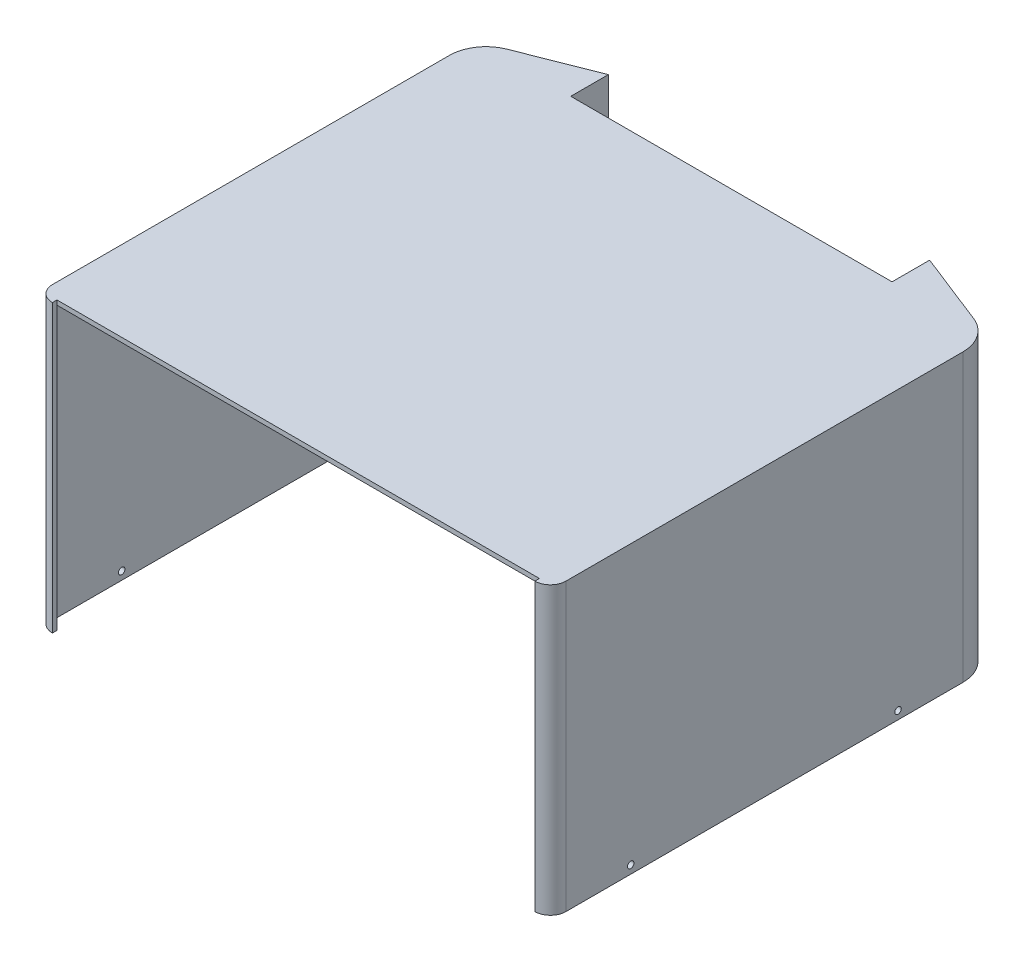
SolidWorks part; units mm, degrees
ref_plane "Front Plane" through (0, 0, 0) normal (0, 0, 1) x (1, 0, 0)
ref_plane "Top Plane" through (0, 0, 0) normal (0, 1, 0) x (1, 0, 0)
ref_plane "Right Plane" through (0, 0, 0) normal (1, 0, 0) x (0, 0, -1)
sketch "Sketch1" plane through (0, 0, 0) normal (0, 1, 0) x (1, 0, 0)
  line L0 (-49.6594, 72.6605) -> (48.7721, 72.6605)
  line L1 (-0.4437, -74.1395) -> (-0.4437, 72.6605)
  line L2 (-49.6594, 59.6605) -> (-50.0594, 59.6605) construction
  line L3 (-50.0594, 59.6605) -> (-49.6594, 59.6605) construction
  line L4 (-72.5188, 63.821) -> (-50.0594, 72.6605)
  line L5 (-79.7437, 53.213) -> (-79.7437, -3.8395)
  line L6 (49.1721, 59.6605) -> (48.7721, 59.6605) construction
  line L7 (48.7721, 59.6605) -> (49.1721, 59.6605) construction
  line L8 (-50.0594, 59.6605) -> (-50.0594, 71.156)
  line L9 (-78.3437, 53.213) -> (-78.3437, -3.8395)
  line L10 (50.5721, 59.6605) -> (50.5721, 70.605)
  line L11 (49.1721, 59.6605) -> (49.1721, 72.6605)
  line L12 (-78.3437, -3.8395) -> (-78.3437, -69.3395)
  line L13 (-74.9437, -72.7395) -> (74.0563, -72.7395)
  line L14 (49.1721, 59.6605) -> (50.5721, 59.6605)
  line L15 (78.8563, -3.8395) -> (78.8563, -69.3395)
  line L16 (71.1187, 62.5183) -> (50.5721, 70.605)
  line L17 (-72.006, 62.5183) -> (-51.4594, 70.605)
  line L18 (-79.7437, -3.8395) -> (-79.7437, -69.3395)
  line L19 (-74.9437, -74.1395) -> (74.0563, -74.1395)
  line L20 (77.4563, -3.8395) -> (77.4563, -69.3395)
  line L21 (77.4563, 53.213) -> (77.4563, -3.8395)
  line L22 (49.1721, 59.6605) -> (49.1721, 71.156)
  line L23 (-50.0594, 59.6605) -> (-51.4594, 59.6605)
  line L24 (-50.0594, 59.6605) -> (-50.0594, 72.6605)
  line L25 (-51.4594, 59.6605) -> (-51.4594, 70.605)
  line L26 (78.8563, 53.213) -> (78.8563, -3.8395)
  line L27 (71.6314, 63.821) -> (49.1721, 72.6605)
  arc A0 (78.8563, -69.3395) -> (74.0563, -74.1395) centre (74.0563, -69.3395) cw
  arc A1 (-78.3437, -69.3395) -> (-74.9437, -72.7395) centre (-74.9437, -69.3395) ccw
  arc A2 (78.8563, 53.213) -> (71.6314, 63.821) centre (67.4563, 53.213) ccw
  arc A3 (-78.3437, 53.213) -> (-72.006, 62.5183) centre (-68.3437, 53.213) cw
  arc A4 (77.4563, 53.213) -> (71.1187, 62.5183) centre (67.4563, 53.213) ccw
  arc A5 (-79.7437, 53.213) -> (-72.5188, 63.821) centre (-68.3437, 53.213) cw
  arc A6 (-79.7437, -69.3395) -> (-74.9437, -74.1395) centre (-74.9437, -69.3395) ccw
  arc A7 (77.4563, -69.3395) -> (74.0563, -72.7395) centre (74.0563, -69.3395) cw
  point P26 (-0.4437, -72.7395)
  dimension "D1" = 10
  dimension "D2" = 1.4
extrude "Boss-Extrude2" add sketch "Sketch1" along normal blind 82 contours L20 A7 L13 L1 L19 A0 L15 L26 A2 L27 L11 L14 L10 L16 A4 L21 | L18 A6 L19 L1 L13 A1 L12 L9 A3 L17 L25 L23 L8 L24 L4 A5 L5
sketch "Sketch3" plane through (0, 82, 0) normal (0, 1, 0) x (1, 0, 0)
  line L0 (-50.0594, 59.6605) -> (49.1721, 59.6605)
  line L16 (77.4563, 53.213) -> (77.4563, -69.3395)
  line L17 (74.0563, -72.7395) -> (-74.9437, -72.7395)
  line L18 (-78.3437, -69.3395) -> (-78.3437, 53.213)
  line L19 (-72.006, 62.5183) -> (-51.4594, 70.605)
  line L20 (-51.4594, 70.605) -> (-51.4594, 59.6605)
  line L21 (-51.4594, 59.6605) -> (-50.0594, 59.6605)
  line L22 (-50.0594, 59.6605) -> (-50.0594, 72.6605)
  line L23 (-50.0594, 72.6605) -> (-72.5188, 63.821)
  line L24 (-79.7437, 53.213) -> (-79.7437, -69.3395)
  line L25 (-74.9437, -74.1395) -> (74.0563, -74.1395)
  line L26 (78.8563, -69.3395) -> (78.8563, 53.213)
  line L27 (71.6314, 63.821) -> (49.1721, 72.6605)
  line L28 (49.1721, 72.6605) -> (49.1721, 59.6605)
  line L29 (49.1721, 59.6605) -> (50.5721, 59.6605)
  line L30 (50.5721, 59.6605) -> (50.5721, 70.605)
  line L31 (50.5721, 70.605) -> (71.1187, 62.5183)
  line L32 (77.4563, 53.213) -> (77.4563, -69.3395)
  line L33 (74.0563, -72.7395) -> (-74.9437, -72.7395)
  line L34 (-78.3437, -69.3395) -> (-78.3437, 53.213)
  line L35 (-72.006, 62.5183) -> (-51.4594, 70.605)
  line L36 (-51.4594, 70.605) -> (-51.4594, 59.6605)
  line L37 (-51.4594, 59.6605) -> (-50.0594, 59.6605)
  line L38 (-50.0594, 59.6605) -> (-50.0594, 72.6605)
  line L39 (-50.0594, 72.6605) -> (-72.5188, 63.821)
  line L40 (-79.7437, 53.213) -> (-79.7437, -69.3395)
  line L41 (-74.9437, -74.1395) -> (74.0563, -74.1395)
  line L42 (78.8563, -69.3395) -> (78.8563, 53.213)
  line L43 (71.6314, 63.821) -> (49.1721, 72.6605)
  line L44 (49.1721, 72.6605) -> (49.1721, 59.6605)
  line L45 (49.1721, 59.6605) -> (50.5721, 59.6605)
  line L46 (50.5721, 59.6605) -> (50.5721, 70.605)
  line L47 (50.5721, 70.605) -> (71.1187, 62.5183)
  arc A8 (74.0563, -72.7395) -> (77.4563, -69.3395) centre (74.0563, -69.3395) ccw
  arc A9 (-78.3437, -69.3395) -> (-74.9437, -72.7395) centre (-74.9437, -69.3395) ccw
  arc A10 (-72.006, 62.5183) -> (-78.3437, 53.213) centre (-68.3437, 53.213) ccw
  arc A11 (-72.5188, 63.821) -> (-79.7437, 53.213) centre (-68.3437, 53.213) ccw
  arc A12 (-79.7437, -69.3395) -> (-74.9437, -74.1395) centre (-74.9437, -69.3395) ccw
  arc A13 (74.0563, -74.1395) -> (78.8563, -69.3395) centre (74.0563, -69.3395) ccw
  arc A14 (78.8563, 53.213) -> (71.6314, 63.821) centre (67.4563, 53.213) ccw
  arc A15 (77.4563, 53.213) -> (71.1187, 62.5183) centre (67.4563, 53.213) ccw
  arc A16 (74.0563, -72.7395) -> (77.4563, -69.3395) centre (74.0563, -69.3395) ccw
  arc A17 (-78.3437, -69.3395) -> (-74.9437, -72.7395) centre (-74.9437, -69.3395) ccw
  arc A18 (-72.006, 62.5183) -> (-78.3437, 53.213) centre (-68.3437, 53.213) ccw
  arc A19 (-72.5188, 63.821) -> (-79.7437, 53.213) centre (-68.3437, 53.213) ccw
  arc A20 (-79.7437, -69.3395) -> (-74.9437, -74.1395) centre (-74.9437, -69.3395) ccw
  arc A21 (74.0563, -74.1395) -> (78.8563, -69.3395) centre (74.0563, -69.3395) ccw
  arc A22 (78.8563, 53.213) -> (71.6314, 63.821) centre (67.4563, 53.213) ccw
  arc A23 (77.4563, 53.213) -> (71.1187, 62.5183) centre (67.4563, 53.213) ccw
  line M25 (77.4563, 53.213) -> (77.4563, -69.3395)
  arc M26 (77.4563, -69.3395) -> (74.0563, -72.7395) centre (74.0563, -69.3395) cw
  line M27 (74.0563, -72.7395) -> (-74.9437, -72.7395)
  arc M28 (-74.9437, -72.7395) -> (-78.3437, -69.3395) centre (-74.9437, -69.3395) cw
  line M29 (-78.3437, -69.3395) -> (-78.3437, 53.213)
  arc M30 (-78.3437, 53.213) -> (-72.006, 62.5183) centre (-68.3437, 53.213) cw
  line M31 (-72.006, 62.5183) -> (-51.4594, 70.605)
  line M32 (-51.4594, 70.605) -> (-51.4594, 59.6605)
  line M33 (-51.4594, 59.6605) -> (-50.0594, 59.6605)
  line M45 (49.1721, 59.6605) -> (50.5721, 59.6605)
  line M46 (50.5721, 59.6605) -> (50.5721, 70.605)
  line M47 (50.5721, 70.605) -> (71.1187, 62.5183)
  arc M48 (71.1187, 62.5183) -> (77.4563, 53.213) centre (67.4563, 53.213) cw
  dimension "D1" = 0
extrude "Boss-Extrude3" add sketch "Sketch3" against normal blind 1.5 contours L0 M33 M32 M31 M30 M29 M28 M27 M26 M25 M48 M47 M46 M45
sketch "Sketch4" plane through (0, 0, 74.1395) normal (0, 0, 1) x (1, 0, 0)
  line L4 (-74.9437, 0) -> (74.0563, 0)
  line L5 (74.0563, 0) -> (74.0563, 82)
  line L6 (74.0563, 82) -> (-74.9437, 82)
  line L7 (-74.9437, 82) -> (-74.9437, 0)
  line L8 (-74.9437, 0) -> (74.0563, 0)
  line L9 (74.0563, 0) -> (74.0563, 82)
  line L10 (74.0563, 82) -> (-74.9437, 82)
  line L11 (-74.9437, 82) -> (-74.9437, 0)
  dimension "D1" = 0
extrude "Cut-Extrude2" cut sketch "Sketch4" against normal blind 1.5
sketch "Sketch5" plane through (0, 82, 0) normal (0, 1, 0) x (1, 0, 0)
  line L0 (-50.0594, 59.6605) -> (-50.0594, 59.4605)
  line L1 (-50.0594, 59.6605) -> (49.1721, 59.6605)
  line L2 (-50.0594, 59.4605) -> (49.1721, 59.4605)
  line L3 (49.1721, 59.6605) -> (49.1721, 59.4605)
  line L4 (49.1721, 59.6605) -> (49.1721, 72.6605) construction
  dimension "D1" = 0.2
extrude "Cut-Extrude3" cut sketch "Sketch5" against normal blind 18
sketch "Sketch6" plane through (-79.7437, 0, 0) normal (-1, 0, 0) x (0, 0, 1)
  line L1 (69.3395, 5) -> (49.3395, 5) construction
  line L2 (69.3395, 82) -> (69.3395, 0) construction
  line L3 (-53.213, 5) -> (-33.213, 5) construction
  line L4 (-53.213, 82) -> (-53.213, 0) construction
  line L5 (-53.213, 0) -> (69.3395, 0) construction
  line L6 (-33.213, 5) -> (-33.213, 0) construction
  line L7 (49.3395, 5) -> (49.3395, 0) construction
  circle A0 centre (-33.213, 2.5) radius 1
  circle A1 centre (49.3395, 2.5) radius 1
  dimension "D4" = 2
  dimension "D5" = 2
  dimension "D1" = 5
  dimension "D2" = 20
  dimension "D3" = 20
extrude "Cut-Extrude4" cut sketch "Sketch6" against normal blind 243
sketch "Sketch7" plane through (0, 80.5, 0) normal (0, -1, 0) x (1, 0, 0)
  line L14 (-50.0594, -59.4605) -> (49.1721, -59.4605)
  line L15 (49.1721, -59.4605) -> (49.1721, -59.6605)
  line L16 (49.1721, -59.6605) -> (50.5721, -59.6605)
  line L17 (50.5721, -59.6605) -> (50.5721, -70.605)
  line L18 (50.5721, -70.605) -> (71.1187, -62.5183)
  line L19 (77.4563, -53.213) -> (77.4563, 69.3395)
  line L20 (74.0563, 72.7395) -> (74.0563, 72.6395)
  line L21 (74.0563, 72.6395) -> (-74.9437, 72.6395)
  line L22 (-74.9437, 72.6395) -> (-74.9437, 72.7395)
  line L23 (-78.3437, 69.3395) -> (-78.3437, -53.213)
  line L24 (-72.006, -62.5183) -> (-51.4594, -70.605)
  line L25 (-51.4594, -70.605) -> (-51.4594, -59.6605)
  line L26 (-51.4594, -59.6605) -> (-50.0594, -59.6605)
  line L27 (-50.0594, -59.6605) -> (-50.0594, -59.4605)
  line L28 (-50.0594, -59.4605) -> (49.1721, -59.4605)
  line L29 (49.1721, -59.4605) -> (49.1721, -59.6605)
  line L30 (49.1721, -59.6605) -> (50.5721, -59.6605)
  line L31 (50.5721, -59.6605) -> (50.5721, -70.605)
  line L32 (50.5721, -70.605) -> (71.1187, -62.5183)
  line L33 (77.4563, -53.213) -> (77.4563, 69.3395)
  line L34 (74.0563, 72.7395) -> (74.0563, 72.6395)
  line L35 (74.0563, 72.6395) -> (-74.9437, 72.6395)
  line L36 (-74.9437, 72.6395) -> (-74.9437, 72.7395)
  line L37 (-78.3437, 69.3395) -> (-78.3437, -53.213)
  line L38 (-72.006, -62.5183) -> (-51.4594, -70.605)
  line L39 (-51.4594, -70.605) -> (-51.4594, -59.6605)
  line L40 (-51.4594, -59.6605) -> (-50.0594, -59.6605)
  line L41 (-50.0594, -59.6605) -> (-50.0594, -59.4605)
  arc A4 (71.1187, -62.5183) -> (77.4563, -53.213) centre (67.4563, -53.213) ccw
  arc A5 (77.4563, 69.3395) -> (74.0563, 72.7395) centre (74.0563, 69.3395) ccw
  arc A6 (-74.9437, 72.7395) -> (-78.3437, 69.3395) centre (-74.9437, 69.3395) ccw
  arc A7 (-78.3437, -53.213) -> (-72.006, -62.5183) centre (-68.3437, -53.213) ccw
  arc A8 (71.1187, -62.5183) -> (77.4563, -53.213) centre (67.4563, -53.213) ccw
  arc A9 (77.4563, 69.3395) -> (74.0563, 72.7395) centre (74.0563, 69.3395) ccw
  arc A10 (-74.9437, 72.7395) -> (-78.3437, 69.3395) centre (-74.9437, 69.3395) ccw
  arc A11 (-78.3437, -53.213) -> (-72.006, -62.5183) centre (-68.3437, -53.213) ccw
  dimension "D1" = 0
extrude "Cut-Extrude5" cut sketch "Sketch7" against normal blind 16.4
sketch "Sketch8" plane through (0, 82, 0) normal (0, 1, 0) x (1, 0, 0)
  line L0 (74.0563, -72.7395) -> (74.0563, -74.1395) construction
  line L1 (78.8563, -69.3395) -> (78.8563, 53.213) construction
  line L2 (71.6314, 63.821) -> (49.1721, 72.6605) construction
  line L3 (49.1721, 72.6605) -> (49.1721, 59.6605) construction
  line L4 (49.1721, 59.6605) -> (50.5721, 59.6605) construction
  line L5 (50.5721, 59.6605) -> (50.5721, 70.605) construction
  line L6 (50.5721, 70.605) -> (71.1187, 62.5183) construction
  line L7 (77.4563, 53.213) -> (77.4563, -69.3395) construction
  line L8 (-51.4594, 59.6605) -> (-50.0594, 59.6605) construction
  line L9 (-50.0594, 59.6605) -> (-50.0594, 72.6605) construction
  line L10 (-50.0594, 72.6605) -> (-72.5188, 63.821) construction
  line L11 (-79.7437, 53.213) -> (-79.7437, -69.3395) construction
  line L12 (-74.9437, -74.1395) -> (-74.9437, -72.7395) construction
  line L13 (-78.3437, -69.3395) -> (-78.3437, 53.213) construction
  line L14 (-72.006, 62.5183) -> (-51.4594, 70.605) construction
  line L15 (-51.4594, 70.605) -> (-51.4594, 59.6605) construction
  line L16 (74.0563, -72.7395) -> (74.0563, -74.1395)
  line L17 (78.8563, -69.3395) -> (78.8563, 53.213)
  line L18 (71.6314, 63.821) -> (49.1721, 72.6605)
  line L19 (49.1721, 72.6605) -> (49.1721, 59.6605)
  line L20 (49.1721, 59.6605) -> (50.5721, 59.6605)
  line L21 (50.5721, 59.6605) -> (50.5721, 70.605)
  line L22 (50.5721, 70.605) -> (71.1187, 62.5183)
  line L23 (77.4563, 53.213) -> (77.4563, -69.3395)
  line L24 (-51.4594, 59.6605) -> (-50.0594, 59.6605)
  line L25 (-50.0594, 59.6605) -> (-50.0594, 72.6605)
  line L26 (-50.0594, 72.6605) -> (-72.5188, 63.821)
  line L27 (-79.7437, 53.213) -> (-79.7437, -69.3395)
  line L28 (-74.9437, -74.1395) -> (-74.9437, -72.7395)
  line L29 (-78.3437, -69.3395) -> (-78.3437, 53.213)
  line L30 (-72.006, 62.5183) -> (-51.4594, 70.605)
  line L31 (-51.4594, 70.605) -> (-51.4594, 59.6605)
  arc A0 (74.0563, -72.7395) -> (77.4563, -69.3395) centre (74.0563, -69.3395) ccw construction
  arc A1 (74.0563, -74.1395) -> (78.8563, -69.3395) centre (74.0563, -69.3395) ccw construction
  arc A2 (78.8563, 53.213) -> (71.6314, 63.821) centre (67.4563, 53.213) ccw construction
  arc A3 (77.4563, 53.213) -> (71.1187, 62.5183) centre (67.4563, 53.213) ccw construction
  arc A4 (-72.5188, 63.821) -> (-79.7437, 53.213) centre (-68.3437, 53.213) ccw construction
  arc A5 (-79.7437, -69.3395) -> (-74.9437, -74.1395) centre (-74.9437, -69.3395) ccw construction
  arc A6 (-78.3437, -69.3395) -> (-74.9437, -72.7395) centre (-74.9437, -69.3395) ccw construction
  arc A7 (-72.006, 62.5183) -> (-78.3437, 53.213) centre (-68.3437, 53.213) ccw construction
  arc A8 (74.0563, -72.7395) -> (77.4563, -69.3395) centre (74.0563, -69.3395) ccw
  arc A9 (74.0563, -74.1395) -> (78.8563, -69.3395) centre (74.0563, -69.3395) ccw
  arc A10 (78.8563, 53.213) -> (71.6314, 63.821) centre (67.4563, 53.213) ccw
  arc A11 (77.4563, 53.213) -> (71.1187, 62.5183) centre (67.4563, 53.213) ccw
  arc A12 (-72.5188, 63.821) -> (-79.7437, 53.213) centre (-68.3437, 53.213) ccw
  arc A13 (-79.7437, -69.3395) -> (-74.9437, -74.1395) centre (-74.9437, -69.3395) ccw
  arc A14 (-78.3437, -69.3395) -> (-74.9437, -72.7395) centre (-74.9437, -69.3395) ccw
  arc A15 (-72.006, 62.5183) -> (-78.3437, 53.213) centre (-68.3437, 53.213) ccw
extrude "Boss-Extrude4" add sketch "Sketch8" along normal blind 5
sketch "Sketch9" plane through (0, 87, 0) normal (0, 1, 0) x (1, 0, 0)
  line L0 (74.0563, -72.7395) -> (74.0563, -74.1395) construction
  line L1 (78.8563, -69.3395) -> (78.8563, 53.213) construction
  line L2 (71.6314, 63.821) -> (49.1721, 72.6605) construction
  line L3 (49.1721, 72.6605) -> (49.1721, 59.6605) construction
  line L4 (49.1721, 59.6605) -> (50.5721, 59.6605) construction
  line L5 (50.5721, 59.6605) -> (50.5721, 70.605) construction
  line L6 (50.5721, 70.605) -> (71.1187, 62.5183) construction
  line L7 (77.4563, 53.213) -> (77.4563, -69.3395) construction
  line L8 (-51.4594, 70.605) -> (-51.4594, 59.6605) construction
  line L9 (-51.4594, 59.6605) -> (-50.0594, 59.6605) construction
  line L10 (-50.0594, 59.6605) -> (-50.0594, 72.6605) construction
  line L11 (-50.0594, 72.6605) -> (-72.5188, 63.821) construction
  line L12 (-79.7437, 53.213) -> (-79.7437, -69.3395) construction
  line L13 (-74.9437, -74.1395) -> (-74.9437, -72.7395) construction
  line L14 (-78.3437, -69.3395) -> (-78.3437, 53.213) construction
  line L15 (-72.006, 62.5183) -> (-51.4594, 70.605) construction
  line L16 (74.0563, -72.7395) -> (74.0563, -74.1395)
  line L17 (78.8563, -69.3395) -> (78.8563, 53.213)
  line L18 (71.6314, 63.821) -> (49.1721, 72.6605)
  line L19 (49.1721, 72.6605) -> (49.1721, 59.6605)
  line L20 (49.1721, 59.6605) -> (50.5721, 59.6605)
  line L21 (50.5721, 59.6605) -> (50.5721, 70.605)
  line L22 (50.5721, 70.605) -> (71.1187, 62.5183)
  line L23 (77.4563, 53.213) -> (77.4563, -69.3395)
  line L24 (-51.4594, 70.605) -> (-51.4594, 59.6605)
  line L25 (-51.4594, 59.6605) -> (-50.0594, 59.6605)
  line L26 (-50.0594, 59.6605) -> (-50.0594, 72.6605)
  line L27 (-50.0594, 72.6605) -> (-72.5188, 63.821)
  line L28 (-79.7437, 53.213) -> (-79.7437, -69.3395)
  line L29 (-74.9437, -74.1395) -> (-74.9437, -72.7395)
  line L30 (-78.3437, -69.3395) -> (-78.3437, 53.213)
  line L31 (-72.006, 62.5183) -> (-51.4594, 70.605)
  line L32 (-50.0594, 59.6605) -> (49.1721, 59.6605)
  line L33 (74.0563, -72.7395) -> (-74.9437, -72.7395)
  arc A0 (74.0563, -72.7395) -> (77.4563, -69.3395) centre (74.0563, -69.3395) ccw construction
  arc A1 (74.0563, -74.1395) -> (78.8563, -69.3395) centre (74.0563, -69.3395) ccw construction
  arc A2 (78.8563, 53.213) -> (71.6314, 63.821) centre (67.4563, 53.213) ccw construction
  arc A3 (77.4563, 53.213) -> (71.1187, 62.5183) centre (67.4563, 53.213) ccw construction
  arc A4 (-72.5188, 63.821) -> (-79.7437, 53.213) centre (-68.3437, 53.213) ccw construction
  arc A5 (-79.7437, -69.3395) -> (-74.9437, -74.1395) centre (-74.9437, -69.3395) ccw construction
  arc A6 (-78.3437, -69.3395) -> (-74.9437, -72.7395) centre (-74.9437, -69.3395) ccw construction
  arc A7 (-72.006, 62.5183) -> (-78.3437, 53.213) centre (-68.3437, 53.213) ccw construction
  arc A8 (74.0563, -72.7395) -> (77.4563, -69.3395) centre (74.0563, -69.3395) ccw
  arc A9 (74.0563, -74.1395) -> (78.8563, -69.3395) centre (74.0563, -69.3395) ccw
  arc A10 (78.8563, 53.213) -> (71.6314, 63.821) centre (67.4563, 53.213) ccw
  arc A11 (77.4563, 53.213) -> (71.1187, 62.5183) centre (67.4563, 53.213) ccw
  arc A12 (-72.5188, 63.821) -> (-79.7437, 53.213) centre (-68.3437, 53.213) ccw
  arc A13 (-79.7437, -69.3395) -> (-74.9437, -74.1395) centre (-74.9437, -69.3395) ccw
  arc A14 (-78.3437, -69.3395) -> (-74.9437, -72.7395) centre (-74.9437, -69.3395) ccw
  arc A15 (-72.006, 62.5183) -> (-78.3437, 53.213) centre (-68.3437, 53.213) ccw
  line M1 (-51.4594, 70.605) -> (-51.4594, 59.6605)
  line M2 (-51.4594, 59.6605) -> (-50.0594, 59.6605)
  line M3 (-50.0594, 59.6605) -> (-50.0594, 72.6605)
  line M4 (-50.0594, 72.6605) -> (-72.5188, 63.821)
  arc M5 (-72.5188, 63.821) -> (-79.7437, 53.213) centre (-68.3437, 53.213) ccw
  line M6 (-79.7437, 53.213) -> (-79.7437, -69.3395)
  arc M7 (-79.7437, -69.3395) -> (-74.9437, -74.1395) centre (-74.9437, -69.3395) ccw
  line M8 (-74.9437, -74.1395) -> (-74.9437, -72.7395)
  arc M9 (-74.9437, -72.7395) -> (-78.3437, -69.3395) centre (-74.9437, -69.3395) cw
  line M10 (-78.3437, -69.3395) -> (-78.3437, 53.213)
  arc M11 (-78.3437, 53.213) -> (-72.006, 62.5183) centre (-68.3437, 53.213) cw
  line M12 (-72.006, 62.5183) -> (-51.4594, 70.605)
extrude "Boss-Extrude6" add sketch "Sketch9" along normal blind 1.4 contours L23 A11 L22 L21 L20 L32 L33 A8 M2 M1 M12 M11 M10 M9 | M12 M1 M2 M3 M4 M5 M6 M7 M8 M9 M10 M11 | A11 L23 A8 L16 A9 L17 A10 L18 L19 L20 L21 L22
sketch "Sketch10" plane through (0, 0, -59.6605) normal (0, 0, -1) x (-1, 0, 0)
  line L0 (-49.1721, 88.4) -> (-49.1721, 81.66)
  line L1 (-49.1721, 88.4) -> (50.0594, 88.4)
  line L2 (-49.1721, 81.66) -> (50.0594, 81.66)
  line L3 (50.0594, 88.4) -> (50.0594, 81.66)
  line L4 (-49.1721, 87) -> (50.0594, 87)
  line L5 (50.0594, 87) -> (50.0594, 88.4)
  line L6 (50.0594, 88.4) -> (-49.1721, 88.4)
  line L7 (-49.1721, 88.4) -> (-49.1721, 87)
  line L8 (-49.1721, 87) -> (50.0594, 87)
  line L9 (50.0594, 87) -> (50.0594, 88.4)
  line L10 (50.0594, 88.4) -> (-49.1721, 88.4)
  line L11 (-49.1721, 88.4) -> (-49.1721, 87)
  line L12 (-49.1721, 88.4) -> (-49.1721, 0) construction
  line M7 (-49.1721, 87) -> (50.0594, 87)
  line M8 (50.0594, 87) -> (50.0594, 88.4)
  line M9 (50.0594, 88.4) -> (-49.1721, 88.4)
  line M10 (-49.1721, 88.4) -> (-49.1721, 87)
  dimension "D2" = 6.74
  dimension "D1" = 0
extrude "Boss-Extrude7" add sketch "Sketch10" along normal blind 1.4 contours L3 L0 L2 M7 | M10 M7 M8 M9
